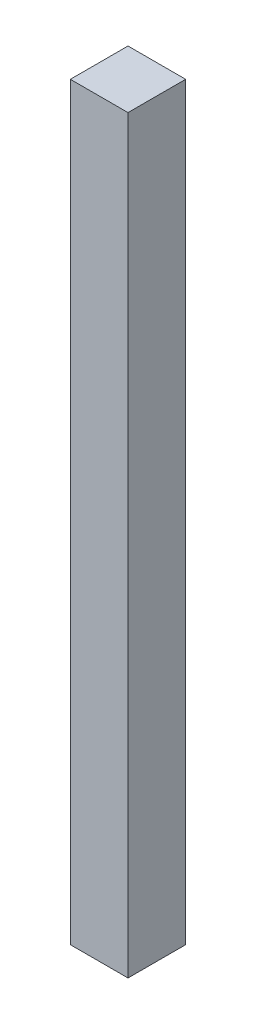
SolidWorks part; units mm, degrees
ref_plane "Plan de face" through (0, 0, 0) normal (0, 0, 1) x (1, 0, 0)
ref_plane "Plan de dessus" through (0, 0, 0) normal (0, 1, 0) x (1, 0, 0)
ref_plane "Plan de droite" through (0, 0, 0) normal (1, 0, 0) x (0, 0, -1)
sketch "Esquisse1" plane through (0, 0, 0) normal (0, 1, 0) x (1, 0, 0)
  line L1 (0, 0) -> (-20, 0)
  line L2 (0, 0) -> (0, 20)
  line L3 (0, 20) -> (-20, 20)
  line L4 (-20, 0) -> (-20, 20)
  dimension "D1" = 20
  dimension "D2" = 20
extrude "Boss.-Extru.1" add sketch "Esquisse1" along normal blind 260
